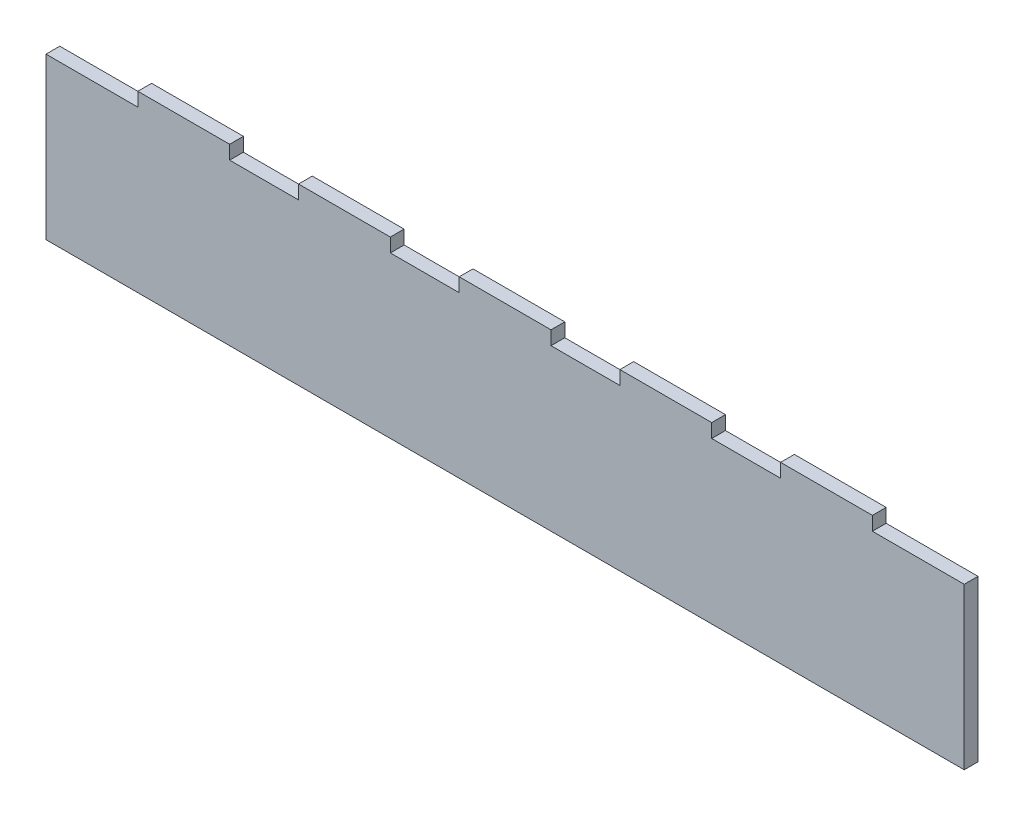
SolidWorks part; units mm, degrees
ref_plane "Front Plane" through (0, 0, 0) normal (0, 0, 1) x (1, 0, 0)
ref_plane "Top Plane" through (0, 0, 0) normal (0, 1, 0) x (1, 0, 0)
ref_plane "Right Plane" through (0, 0, 0) normal (1, 0, 0) x (0, 0, -1)
sketch "Sketch1" plane through (0, 0, 0) normal (0, 0, -1) x (1, 0, 0)
  line L0 (40, 0) -> (55, 0)
  line L1 (0, 0) -> (20, 0)
  line L2 (0, 0) -> (0, 35)
  line L3 (0, 35) -> (200, 35)
  line L4 (200, 0) -> (200, 35)
  line L5 (0, 0) -> (200, 35) construction
  line L6 (0, 35) -> (200, 0) construction
  line L7 (55, -3) -> (75, -3)
  line L8 (20, 0) -> (20, -3)
  line L9 (20, -3) -> (40, -3)
  line L10 (40, 0) -> (40, -3)
  line L11 (75, 0) -> (75, -3)
  line L12 (55, 0) -> (55, -3)
  line L13 (90, -3) -> (110, -3)
  line L14 (110, 0) -> (110, -3)
  line L15 (90, 0) -> (90, -3)
  line L16 (125, -3) -> (145, -3)
  line L17 (145, 0) -> (145, -3)
  line L18 (125, 0) -> (125, -3)
  line L19 (160, -3) -> (180, -3)
  line L20 (180, 0) -> (180, -3)
  line L21 (160, 0) -> (160, -3)
  line L22 (75, 0) -> (90, 0)
  line L23 (110, 0) -> (125, 0)
  line L24 (145, 0) -> (160, 0)
  line L25 (180, 0) -> (200, 0)
  point P4 (100, 17.5)
  point P10 (25.3866, 2.1907)
  dimension "D1" = 20
  dimension "D2" = 20
  dimension "D3" = 3
  dimension "D4" = 200
  dimension "D5" = 35
  dimension "D7" = 15
  dimension "D6" = 5
extrude "Boss-Extrude1" add sketch "Sketch1" along normal blind 3 contours L3 L4 L25 L20 L19 L21 L24 L17 L16 L18 L23 L14 L13 L15 L22 L11 L7 L12 L0 L10 L9 L8 L1 L2
